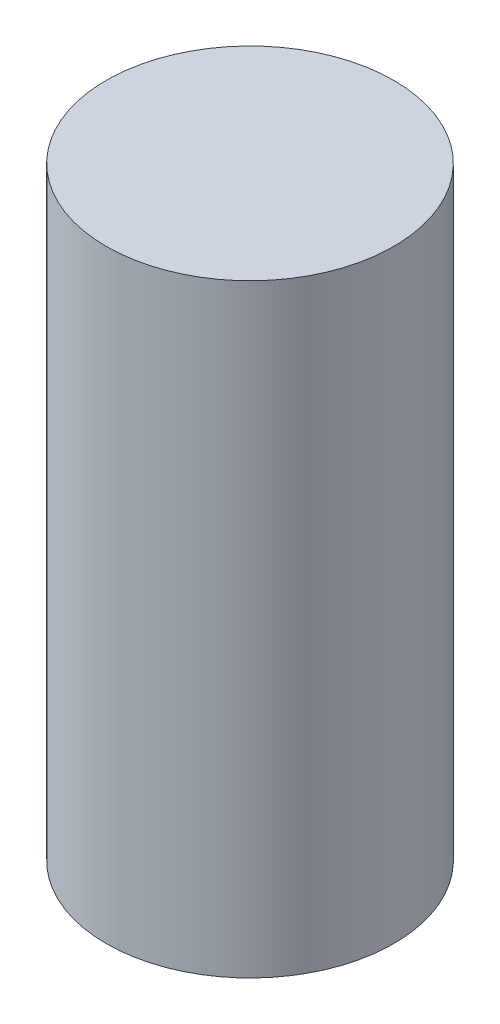
SolidWorks part; units mm, degrees
material "Plain Carbon Steel"
ref_plane "Front Plane" through (0, 0, 0) normal (0, 0, 1) x (1, 0, 0)
ref_plane "Top Plane" through (0, 0, 0) normal (0, 1, 0) x (1, 0, 0)
ref_plane "Right Plane" through (0, 0, 0) normal (1, 0, 0) x (0, 0, -1)
sketch "Sketch1" plane through (0, 0, 0) normal (0, 1, 0) x (1, 0, 0)
  circle A0 centre (0, 0) radius 2.3813
  dimension "D1" = 4.7625
extrude "Boss-Extrude1" add sketch "Sketch1" along normal blind 10
